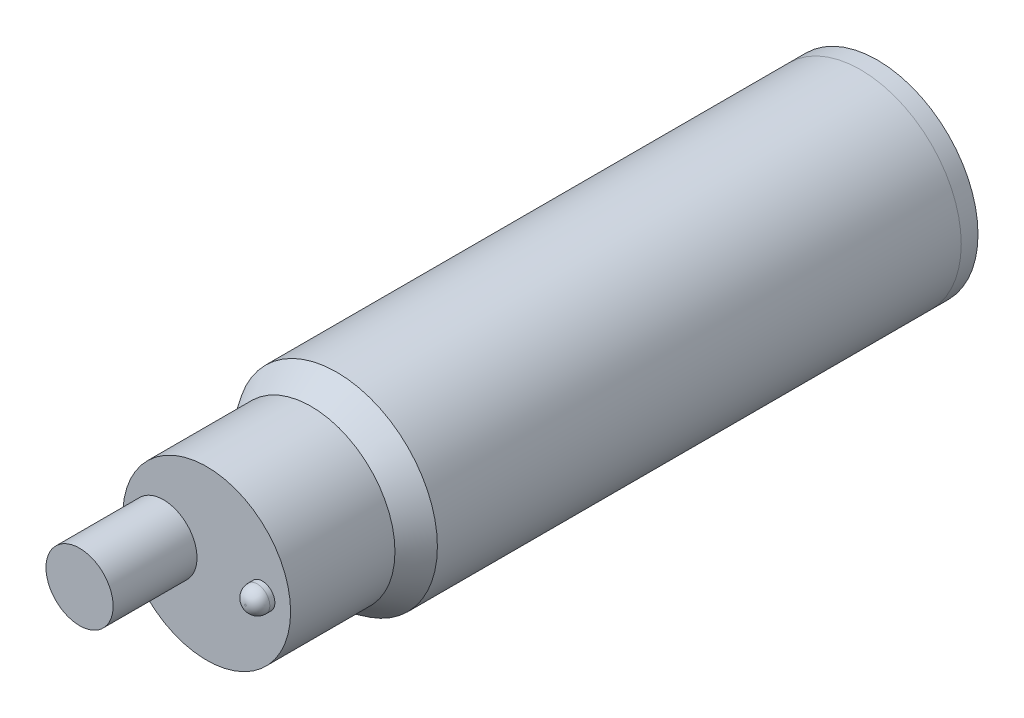
SolidWorks part; units mm, degrees
ref_plane "Front Plane" through (0, 0, 0) normal (0, 0, 1) x (1, 0, 0)
ref_plane "Top Plane" through (0, 0, 0) normal (0, 1, 0) x (1, 0, 0)
ref_plane "Right Plane" through (0, 0, 0) normal (1, 0, 0) x (0, 0, -1)
sketch "Sketch1" plane through (0, 0, 0) normal (0, 1, 0) x (1, 0, 0)
  line L0 (0, 31.22) -> (0, 0)
  line L1 (0, 0) -> (1, -1.5285)
  line L2 (1, -1.5285) -> (1, -7.7485)
  line L3 (1, -7.7485) -> (6, -7.7485)
  line L4 (6, -7.7485) -> (6, 31.22)
  line L7 (0, 31.22) -> (6, 31.22)
  dimension "D1" = 31.22
  dimension "D2" = 6
  dimension "D3" = 6.22
  dimension "D4" = 1
revolve "Revolve1" add sketch "Sketch1" angle 360 about L4
sketch "Sketch2" plane through (0, 0, 7.7485) normal (0, 0, 1) x (1, 0, 0)
  circle A0 centre (9.311, 0) radius 0.75
  dimension "D1" = 1.5
extrude "Boss-Extrude1" add sketch "Sketch2" along normal blind 1
fillet "Fillet1" radius 0.7 1 edges at (10.061, 0, 8.7485)
sketch "Sketch3" plane through (0, 0, 7.7485) normal (0, 0, 1) x (1, 0, 0)
  circle A0 centre (3.423, 0) radius 2
extrude "Boss-Extrude2" add sketch "Sketch3" along normal blind 5
sketch "Sketch4" plane through (0, 0, -31.22) normal (0, 0, -1) x (-1, 0, 0)
  circle A0 centre (-5.997, 0) radius 6
extrude "Boss-Extrude3" add sketch "Sketch4" along normal blind 1
